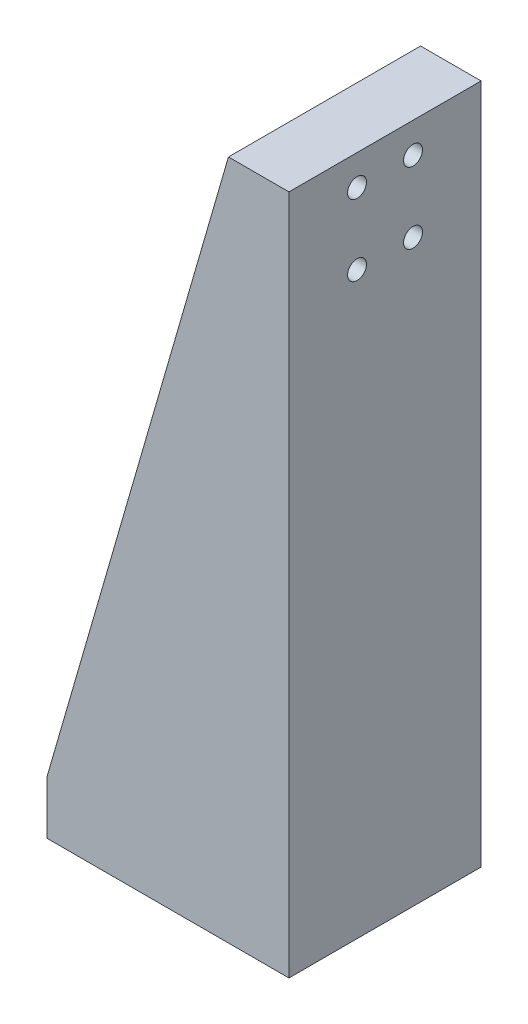
SolidWorks part; units mm, degrees
ref_plane "Front Plane" through (0, 0, 0) normal (0, 0, 1) x (1, 0, 0)
ref_plane "Top Plane" through (0, 0, 0) normal (0, 1, 0) x (1, 0, 0)
ref_plane "Right Plane" through (0, 0, 0) normal (1, 0, 0) x (0, 0, -1)
sketch "Sketch1" plane through (0, 0, 0) normal (0, 0, 1) x (1, 0, 0)
  line L0 (0, 0) -> (0, 7)
  line L1 (0, 7) -> (24, 7)
  line L2 (24, 7) -> (24, 90)
  line L3 (24, 90) -> (32, 90)
  line L4 (32, 90) -> (32, 0)
  line L5 (32, 0) -> (0, 0)
  dimension "D1" = 90
  dimension "D2" = 32
  dimension "D3" = 7
  dimension "D4" = 8
extrude "Boss-Extrude1" add sketch "Sketch1" along normal blind 25.4
ref_plane "Plane4" through (0, 0, 12.7) normal (0, 0, 1) x (1, 0, 0)
sketch "Sketch4" plane through (0, 0, 25.4) normal (0, 0, 1) x (1, 0, 0)
  line L0 (24, 90) -> (0, 7)
rib "Rib1" sketch "Sketch4" sketch "Sketch4" thickness 5 extrusion direction parallel to sketch draft on no parameters "D1"=5
mirror "Mirror1" about plane through (0, 0, 12.7) normal (0, 0, 1) of "Rib1"
sketch "Sketch5" plane through (0, 7, 0) normal (0, 1, 0) x (1, 0, 0)
  line L0 (4, -9) -> (0, -9) construction
  line L1 (4, -9) -> (20, -9) construction
  line L2 (4, -9) -> (4, -16.4) construction
  line L3 (4, -16.4) -> (20, -16.4) construction
  line L4 (20, -9) -> (20, -16.4) construction
  line L5 (0, -20.4) -> (0, -5) construction
  line L6 (4, -9) -> (4, -5) construction
  line L7 (0, -5) -> (24, -5) construction
  line L8 (20, -16.4) -> (20, -20.4) construction
  line L9 (24, -20.4) -> (0, -20.4) construction
  line L10 (20, -16.4) -> (24, -16.4) construction
  line L11 (24, -20.4) -> (24, -5) construction
  circle A0 centre (4, -9) radius 1.55
  circle A1 centre (20, -9) radius 1.55
  circle A2 centre (20, -16.4) radius 1.55
  circle A3 centre (4, -16.4) radius 1.55
  dimension "D4" = 3.1
  dimension "D1" = 4
  dimension "D2" = 4
  dimension "D3" = 4
extrude "Cut-Extrude2" cut sketch "Sketch5" against normal up to next
hole_wizard "M3 Tapped Hole2" positions "Sketch11" profile "Sketch10" tap size "M3" standard "AS" end condition up to next
sketch "Sketch11" plane through (32, 0, 0) normal (1, 0, 0) x (0, 0, -1)
  line L1 (-16.4, 76.6) -> (-9, 76.6) construction
  line L2 (-16.4, 76.6) -> (-16.4, 86) construction
  line L3 (-16.4, 86) -> (-9, 86) construction
  line L4 (-9, 76.6) -> (-9, 86) construction
  line L5 (-16.4, 76.6) -> (-9, 86) construction
  line L6 (-16.4, 86) -> (-9, 76.6) construction
  line L7 (-12.7, 86) -> (-12.7, 90) construction
  line L8 (-25.4, 90) -> (0, 90) construction
  point P2 (-9, 86)
  point P117 (-16.4, 76.6)
  point P118 (-16.4, 86)
  point P119 (-9, 76.6)
  dimension "D1" = 9.4
  dimension "D2" = 7.4
  dimension "D3" = 4
sketch "Sketch10" plane through (32, 86, 9) normal (0, 1, 0) x (0, 0, -1)
  line L0 (0, 0) -> (0, 8)
  line L1 (0, 8) -> (1.25, 8)
  line L2 (1.25, 8) -> (1.25, 0)
  line L5 (1.25, 0) -> (0, 0)
  line L11 (0, -6.35) -> (0, 107.95) construction
  dimension "Thru Tap Drill Dia." = 2.5
  dimension "Thru Tap Drill Depth" = 8
cosmetic thread "Hole Thread5" parameters "D2"=3
cosmetic thread "Hole Thread6" parameters "D2"=3
cosmetic thread "Hole Thread7" parameters "D2"=3
cosmetic thread "Hole Thread8" parameters "D2"=3
